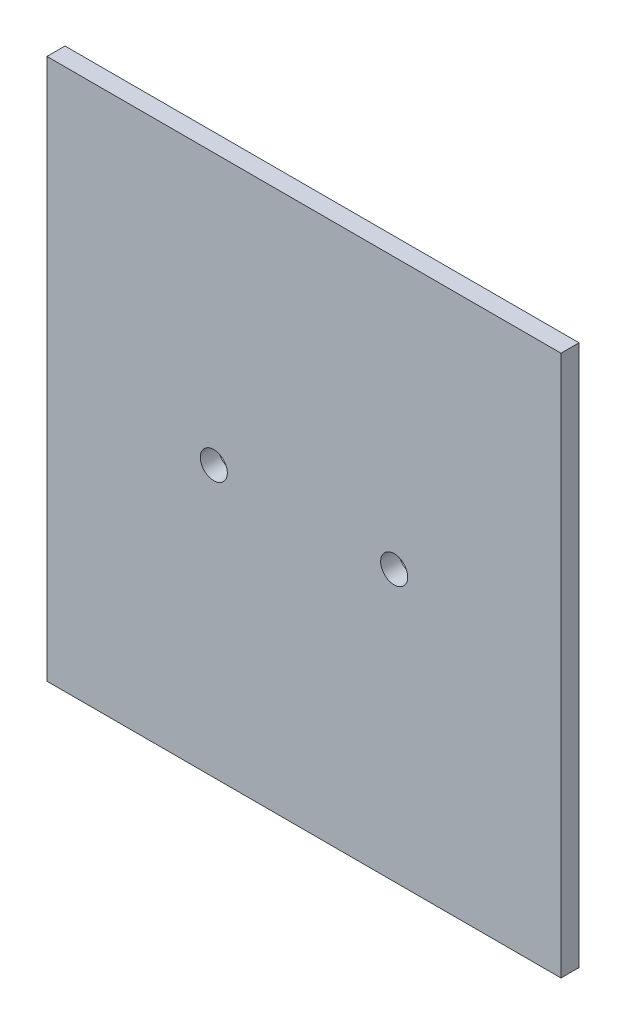
SolidWorks part; units mm, degrees
ref_plane "Front Plane" through (0, 0, 0) normal (0, 0, 1) x (1, 0, 0)
ref_plane "Top Plane" through (0, 0, 0) normal (0, 1, 0) x (1, 0, 0)
ref_plane "Right Plane" through (0, 0, 0) normal (1, 0, 0) x (0, 0, -1)
sketch "Sketch1" plane through (0, 0, 0) normal (0, 0, 1) x (1, 0, 0)
  line L0 (-28.5, 0) -> (28.5, 0) construction
  line L1 (-28.5, -30) -> (28.5, -30)
  line L2 (-28.5, -30) -> (-28.5, 30)
  line L3 (-28.5, 30) -> (28.5, 30)
  line L4 (28.5, -30) -> (28.5, 30)
  line L5 (-28.5, -30) -> (28.5, 30) construction
  line L6 (-28.5, 30) -> (28.5, -30) construction
  circle A0 centre (-10, 0) radius 1.5
  circle A1 centre (10, 0) radius 1.5
  point P0 (0, 0)
  dimension "D3" = 3
  dimension "D4" = 3
  dimension "D1" = 57
  dimension "D2" = 60
  dimension "D5" = 20
  dimension "D6" = 10
extrude "Boss-Extrude1" add sketch "Sketch1" along normal blind 2
